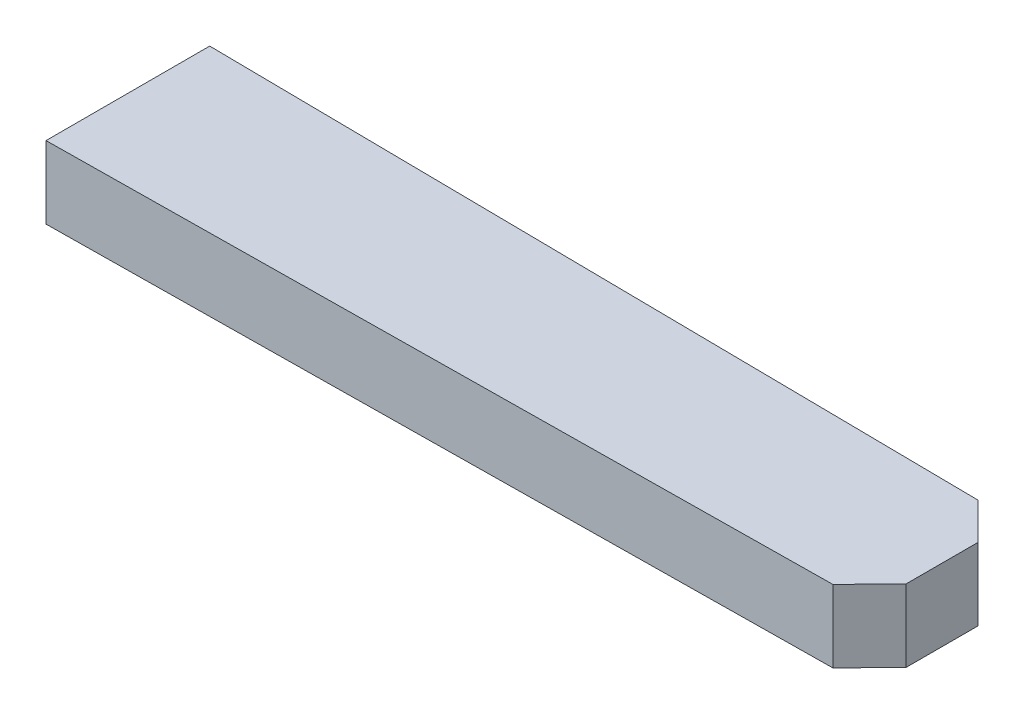
SolidWorks part; units mm, degrees
material "Oak"
ref_plane "Front Plane" through (0, 0, 0) normal (0, 0, 1) x (1, 0, 0)
ref_plane "Top Plane" through (0, 0, 0) normal (0, 1, 0) x (1, 0, 0)
ref_plane "Right Plane" through (0, 0, 0) normal (1, 0, 0) x (0, 0, -1)
sketch "Sketch2" plane through (0, 0, 0) normal (0, 1, 0) x (1, 0, 0)
  line L0 (0, 9.05) -> (45, 8.525)
  line L1 (0, 0) -> (45, 0) construction
  line L2 (0, 0) -> (0, 9.05) construction
  line L3 (0, 9.05) -> (45, 9.05) construction
  line L4 (45, 0) -> (45, 9.05) construction
  line L5 (45, 8.525) -> (45, 0.525)
  line L6 (45, 0.525) -> (0, 0)
  line L7 (0, 9.05) -> (0, 0)
  point P8 (45, 4.525)
  point P9 (45, 4.525)
  dimension "D1" = 45
  dimension "D2" = 9.05
  dimension "D3" = 8
extrude "Boss-Extrude1" add sketch "Sketch2" along normal blind 4
chamfer "Chamfer2" distance 2 angle 45 2 edges at (45, 2, -0.525) (45, 2, -8.525)
